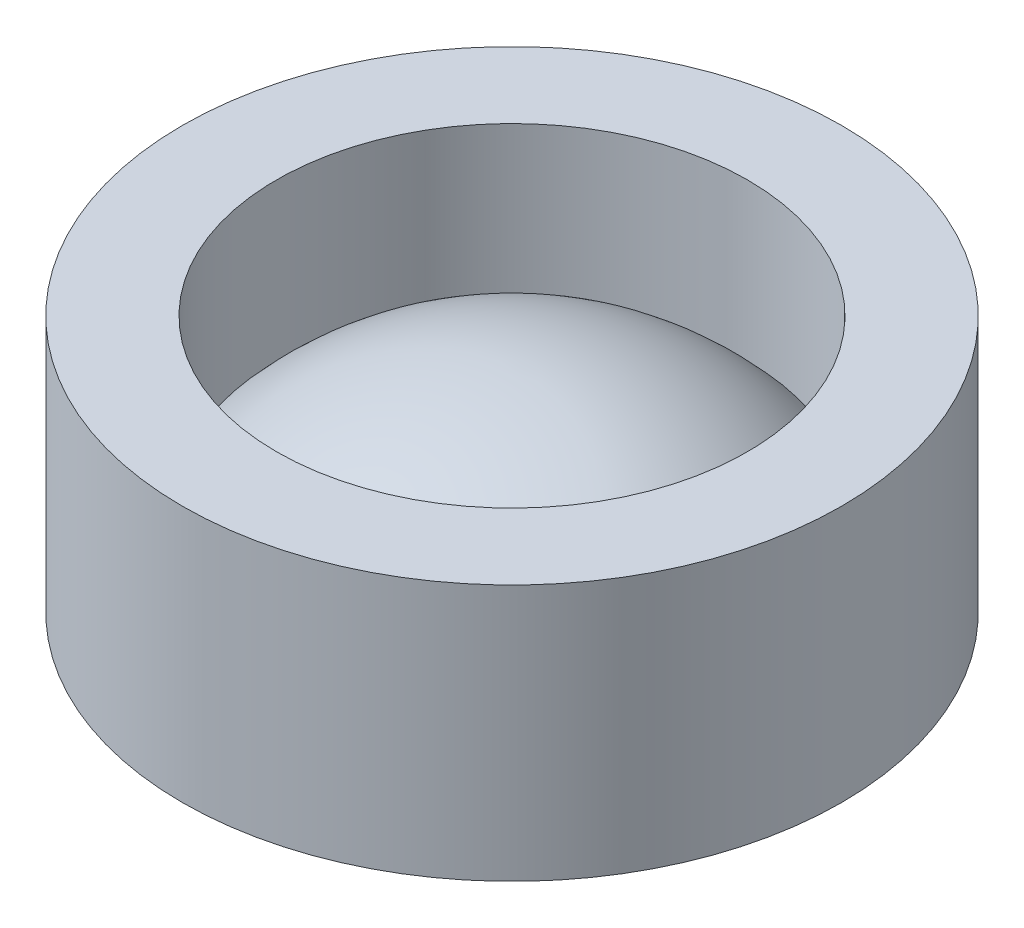
SolidWorks part; units mm, degrees
ref_plane "Front Plane" through (0, 0, 0) normal (0, 0, 1) x (1, 0, 0)
ref_plane "Top Plane" through (0, 0, 0) normal (0, 1, 0) x (1, 0, 0)
ref_plane "Right Plane" through (0, 0, 0) normal (1, 0, 0) x (0, 0, -1)
sketch "Sketch1" plane through (0, 0, 0) normal (0, 1, 0) x (1, 0, 0)
  circle A0 centre (0, 0) radius 10.5
  dimension "D1" = 21
extrude "Boss-Extrude1" add sketch "Sketch1" along normal blind 8.1741
sketch "Sketch2" plane through (0, 0, 0) normal (1, 0, 0) x (0, 0, -1)
  line L0 (0, 8.1741) -> (7.5, 8.1741)
  line L1 (7.5, 3.1741) -> (7.5, 8.1741)
  line L3 (0, 8.1741) -> (0, 6.5597)
  line L4 (-3.4624, 6.5597) -> (-16.0416, 6.5597) construction
  arc A2 (7.5, 3.1741) -> (0, 6.5597) centre (0, -3.4403) ccw
  point P3 (0, 5.8004)
  point P8 (0, 0)
  point P9 (0, 0)
  dimension "D4" = 10
  dimension "D1" = 7.5
  dimension "D2" = 8.1741
  dimension "D3" = 5
sketch "Sketch3" plane through (0, 0, 0) normal (0, 0, 1) x (1, 0, 0)
  line L0 (0, 0.0491) -> (0, 9.5041) construction
revolve "Cut-Revolve2" cut sketch "Sketch2" angle 360 about L0
equation "\"radius\"= 7.5 / 1000"
equation "\"D1@Sketch1\"=\"radius\"*2+.006"
equation "\"a\"= - 32.3127"
equation "\"b\"= .15"
equation "\"c\"=0.005"
equation "\"D1@Boss-Extrude1\" = \"depth\""
equation "\"D2@Sketch2\"=\"depth\""
equation "\"critical\"= - \"b\" / 2 / \"a\""
equation "\"critical_height\"= \"c\" + \"b\" * \"critical\" + \"a\" * \"critical\" ^ 2"
equation "\"center_height\"= \"c\""
equation "\"left_height\"= \"c\" + \"b\" * \"radius\" + \"a\" * \"radius\" ^ 2"
equation "\"max_height\"= \"critical_height\""
equation "\"min_height\"= \"center_height\""
equation "\"depth\"= 0.003 + \"c\" + \"max_height\" - \"min_height\""
